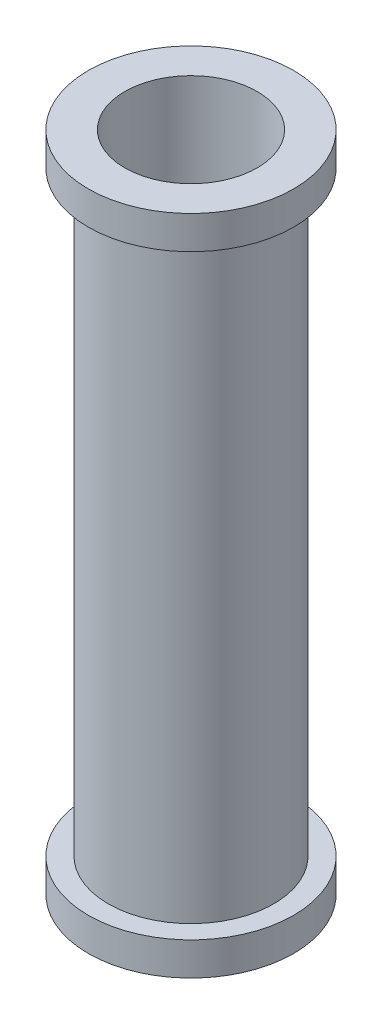
SolidWorks part; units mm, degrees
ref_plane "Front Plane" through (0, 0, 0) normal (0, 0, 1) x (1, 0, 0)
ref_plane "Top Plane" through (0, 0, 0) normal (0, 1, 0) x (1, 0, 0)
ref_plane "Right Plane" through (0, 0, 0) normal (1, 0, 0) x (0, 0, -1)
sketch "Sketch1" plane through (0, 0, 0) normal (0, 0, 1) x (1, 0, 0)
  line L0 (0, 0) -> (0, 1)
sketch "Sketch3" plane through (0, 0, 0) normal (0, 1, 0) x (1, 0, 0)
  circle A0 centre (0, 0) radius 0.2
sweep "Sweep-Thin1" add profiles "Sketch3" path "Sketch1" parameters "D1"=0.05
sketch "Sketch5" plane through (0, 0, 0) normal (0, 0, 1) x (1, 0, 0)
  line L0 (0, 0) -> (0, 0.1)
sketch "Sketch6" plane through (0, 0, 0) normal (0, 1, 0) x (1, 0, 0)
  circle A0 centre (0, 0) radius 0.21
sweep "Sweep-Thin2" add profiles "Sketch6" path "Sketch5" parameters "D1"=0.1
mirror "Mirror2" about plane through (0, 1, 0) normal (0, 1, 0) of bodies 102
